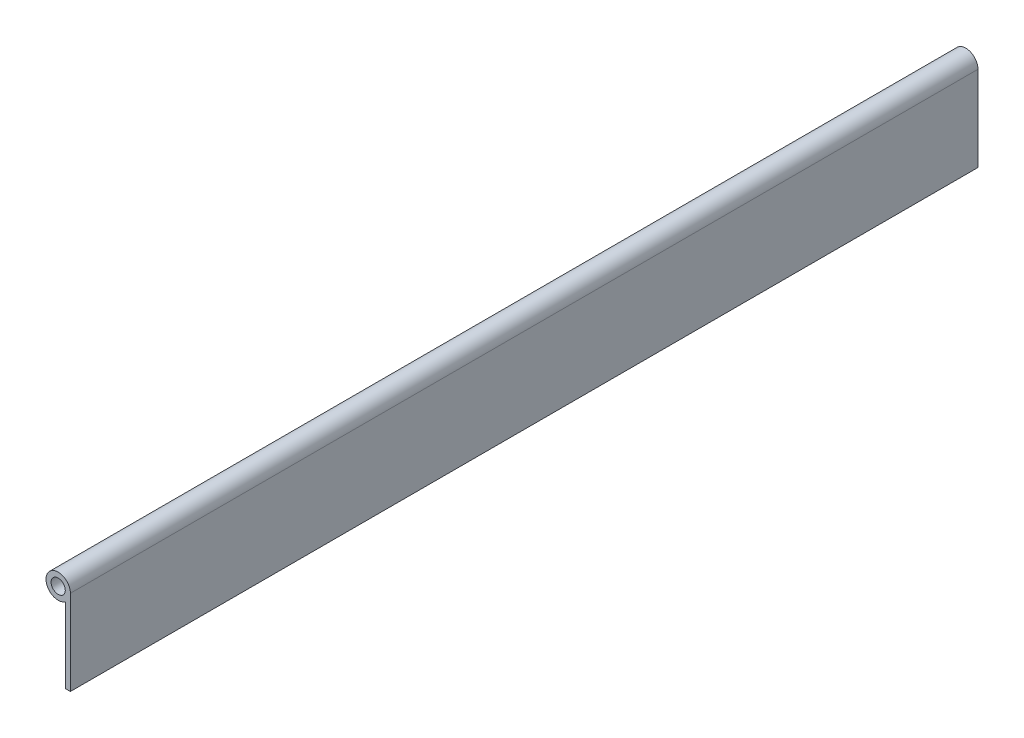
SolidWorks part; units mm, degrees
material "6061 Alloy"
ref_plane "Front Plane" through (0, 0, 0) normal (0, 0, 1) x (1, 0, 0)
ref_plane "Top Plane" through (0, 0, 0) normal (0, 1, 0) x (1, 0, 0)
ref_plane "Right Plane" through (0, 0, 0) normal (1, 0, 0) x (0, 0, -1)
sketch "Sketch1" plane through (0, 0, 0) normal (0, 0, 1) x (1, 0, 0)
  line L0 (5.461, 0) -> (5.461, -38.1)
  line L1 (5.461, -38.1) -> (3.175, -38.1)
  line L2 (3.175, -38.1) -> (3.175, -4.4432)
  circle A0 centre (0, 0) radius 3.175
  arc A1 (5.461, 0) -> (3.175, -4.4432) centre (0, 0) ccw
  circle A2 centre (0, 0) radius 5.461 construction
  dimension "D1" = 6.35
  dimension "D3" = 2.286
  dimension "D4" = 38.1
  dimension "D2" = 2.286
extrude "Boss-Extrude1" add sketch "Sketch1" along normal blind 406.4
sketch "Sketch2" plane through (5.461, 0, 0) normal (1, 0, 0) x (0, 0, -1)
  line L1 (-406.4, 5.461) -> (-381, 5.461)
  line L2 (-406.4, 5.461) -> (-406.4, -7.239)
  line L3 (-406.4, -7.239) -> (-381, -7.239)
  line L4 (-381, 5.461) -> (-381, -7.239)
  dimension "D1" = 12.7
  dimension "D2" = 25.4
extrude "Cut-Extrude1" [suppressed] cut sketch "Sketch2" against normal through all
pattern_linear "LPattern1" [suppressed] count 8 spacing 50.8
sketch "Sketch3" [suppressed] plane through (3.175, 0, 0) normal (-1, 0, 0) x (0, 0, 1)
  line L0 (0, -4.4432) -> (0, -38.1) construction
  line L5 (25.4, -7.239) -> (25.4, -38.1) construction
  line L7 (406.4, -38.1) -> (0, -38.1) construction
  circle A0 centre (25.4, -22.6695) radius 4.7625
  circle A1 centre (203.2, -22.6695) radius 4.7625
  circle A2 centre (381, -22.6695) radius 4.7625
  dimension "D1" = 9.525
  dimension "D2" = 25.4
  dimension "D3" = 3
  dimension "D4" = 177.8
extrude "Cut-Extrude2" [suppressed] cut sketch "Sketch3" against normal through all
